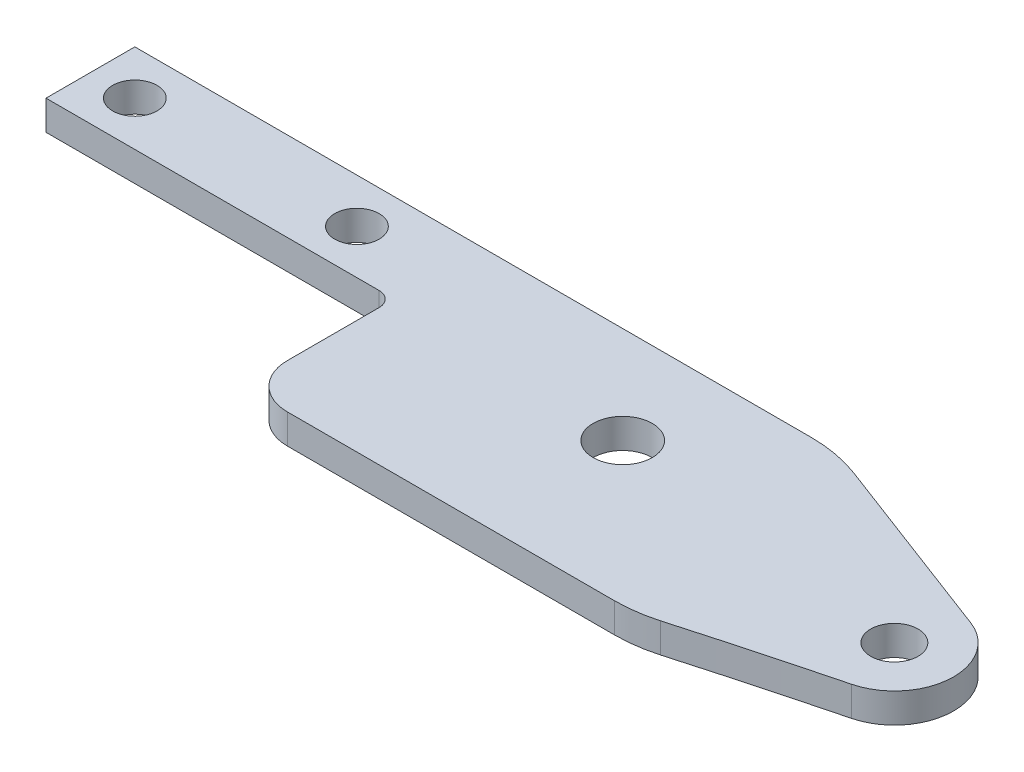
SolidWorks part; units mm, degrees
material "Thornel Mat VMA"
ref_plane "前视基准面" through (0, 0, 0) normal (0, 0, 1) x (1, 0, 0)
ref_plane "上视基准面" through (0, 0, 0) normal (0, 1, 0) x (1, 0, 0)
ref_plane "右视基准面" through (0, 0, 0) normal (1, 0, 0) x (0, 0, -1)
sketch "草图2" plane through (0, 0, 0) normal (0, 1, 0) x (1, 0, 0)
  line L7 (44.5, 3) -> (-3, 3)
  line L8 (-3, 3) -> (-3, -3)
  line L9 (-3, -3) -> (20.5, -3)
  line L17 (15, 0) -> (0, 0) construction
  line L18 (45.5942, -13.2) -> (23.5, -13.2)
  line L20 (58.9165, -2.4592) -> (44.5, 3)
  line L30 (20.5, -3) -> (20.5, -10.2)
  circle A3 centre (0, 0) radius 1.5
  circle A4 centre (15, 0) radius 1.5
  arc A21 (58.489, -10.0758) -> (48.3339, -12.8174) centre (152.4444, -378.2774) ccw
  arc A25 (45.5942, -13.2) -> (48.3339, -12.8174) centre (45.5942, -3.2) ccw
  arc A26 (58.489, -10.0758) -> (58.9165, -2.4592) centre (57.5, -6.2) ccw
  circle A27 centre (57.5, -6.2) radius 1.6
  arc A28 (20.5, -10.2) -> (23.5, -13.2) centre (23.5, -10.2) ccw
  point P2 (-3, 0)
  point P15 (47, -13.2)
  dimension "D4" = 380
  dimension "D6" = 3
  dimension "D7" = 3
  dimension "D8" = 3
  dimension "D11" = 10.2
  dimension "D12" = 47.5
  dimension "D13" = 3
  dimension "D9" = 50
  dimension "D10" = 60.5
  dimension "D15" = 8
  dimension "D17" = 3.2
  dimension "D16" = 10
  dimension "D18" = 7
  dimension "D2" = 23.5
  dimension "D3" = 6
  dimension "D5" = 15
extrude "凸台-拉伸2" add sketch "草图2" along normal blind 2
fillet "圆角1" radius 1 1 edges at (20.5, 1, 3)
fillet "圆角2" radius 10 1 edges at (44.5, 1, -3)
sketch "草图3" plane through (0, 2, 0) normal (0, 1, 0) x (1, 0, 0)
  line L0 (42.67, 3) -> (-3, 3) construction
  line L1 (20.5, -4) -> (20.5, -10.2) construction
  circle A1 centre (36.5, -3.55) radius 2
  dimension "D1" = 4
  dimension "D2" = 6.55
  dimension "D3" = 16
extrude "切除-拉伸1" cut sketch "草图3" against normal through all
